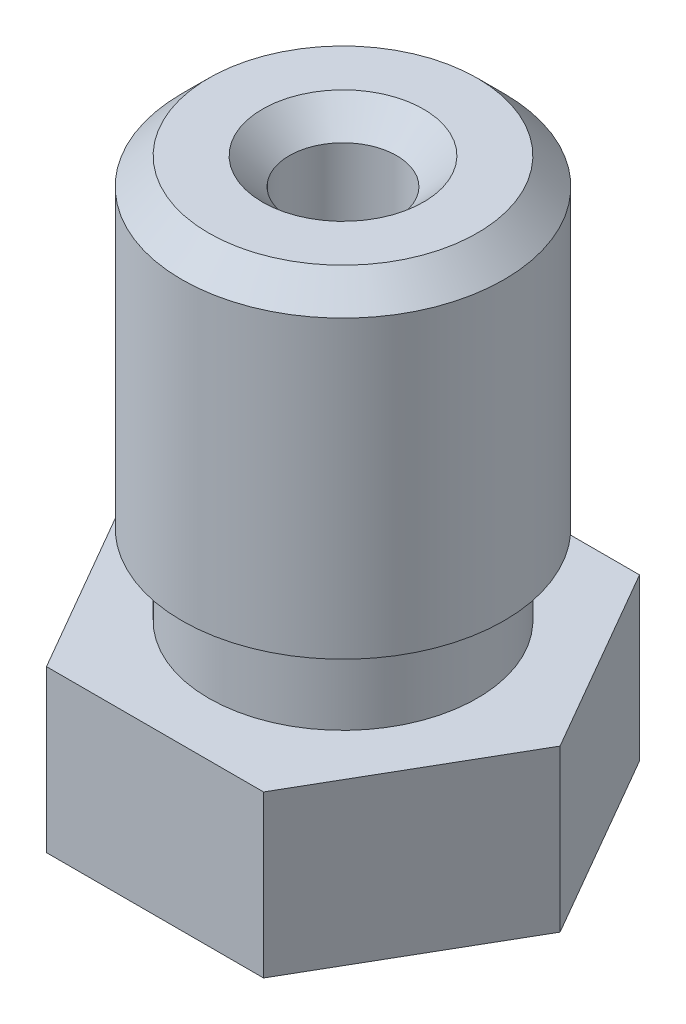
SolidWorks part; units mm, degrees
material "Brass"
ref_plane "Front Plane" through (0, 0, 0) normal (0, 0, 1) x (1, 0, 0)
ref_plane "Top Plane" through (0, 0, 0) normal (0, 1, 0) x (1, 0, 0)
ref_plane "Right Plane" through (0, 0, 0) normal (1, 0, 0) x (0, 0, -1)
ref_plane "Plane1" through (0, 0, 0) normal (0, -1, 0) x (1, 0, 0)
sketch "Sketch1" plane through (0, 0, 0) normal (0, -1, 0) x (1, 0, 0)
  line L0 (-2.0207, 3.5) -> (-4.0415, 0)
  line L1 (-4.0415, 0) -> (-2.0207, -3.5)
  line L2 (-2.0207, -3.5) -> (2.0207, -3.5)
  line L3 (2.0207, -3.5) -> (4.0415, 0)
  line L4 (4.0415, 0) -> (2.0207, 3.5)
  line L5 (2.0207, 3.5) -> (-2.0207, 3.5)
extrude "Boss-Extrude1" add sketch "Sketch1" against normal blind 3
ref_plane "Plane2" through (0, 0, 0) normal (0, 0, -1) x (-1, 0, 0)
sketch "Sketch2" plane through (0, 0, 0) normal (0, 0, -1) x (-1, 0, 0)
  line L0 (-2.5, 3) -> (0, 3)
  line L1 (0, 3) -> (0, 10.5)
  line L2 (0, 10.5) -> (-3, 10.5)
  line L3 (-3, 10.5) -> (-3, 4.5)
  line L4 (-3, 4.5) -> (-2.5, 4.5)
  line L5 (-2.5, 4.5) -> (-2.5, 3)
  line L6 (0, 3) -> (0, 10.5) construction
revolve "Revolve1" add sketch "Sketch2" angle 360 about L6
sketch "Sketch3" plane through (0, 0, 0) normal (0, 0, 1) x (1, 0, 0)
  line L0 (2.5, 0) -> (0, 0)
  line L1 (0, 0) -> (0, -2)
  line L2 (0, -2) -> (0.5, -2)
  line L3 (0.5, -2) -> (2.5, 0)
  line L4 (0, 0) -> (0, -2) construction
revolve "Revolve2" add sketch "Sketch3" angle 360 about L4
sketch "Sketch4" plane through (0, 0, 0) normal (0, 0, -1) x (-1, 0, 0)
  line L0 (-0.3, -2) -> (0, -2)
  line L1 (0, -2) -> (0, 10.5)
  line L2 (0, 10.5) -> (-1, 10.5)
  line L3 (-1, 10.5) -> (-1, 0)
  line L4 (-1, 0) -> (-0.75, -0.2273)
  line L5 (-0.75, -0.2273) -> (-0.75, -0.7)
  line L6 (-0.75, -0.7) -> (-0.3, -1.2)
  line L7 (-0.3, -1.2) -> (-0.3, -2)
  line L8 (0, -2) -> (0, 10.5) construction
  dimension "D1" = 1
  dimension "D2" = 0.3
  dimension "D3" = 0.75
  dimension "D4" = 0.5
  dimension "D5" = 0.8
  dimension "D6" = 0.2273
  dimension "D7" = 0.4727
revolve "Cut-Revolve1" cut sketch "Sketch4" angle 360 about L8
chamfer "Chamfer1" distance 0.5 angle 45 2 edges at (0, 10.5, 3) (0, 10.5, 1)
